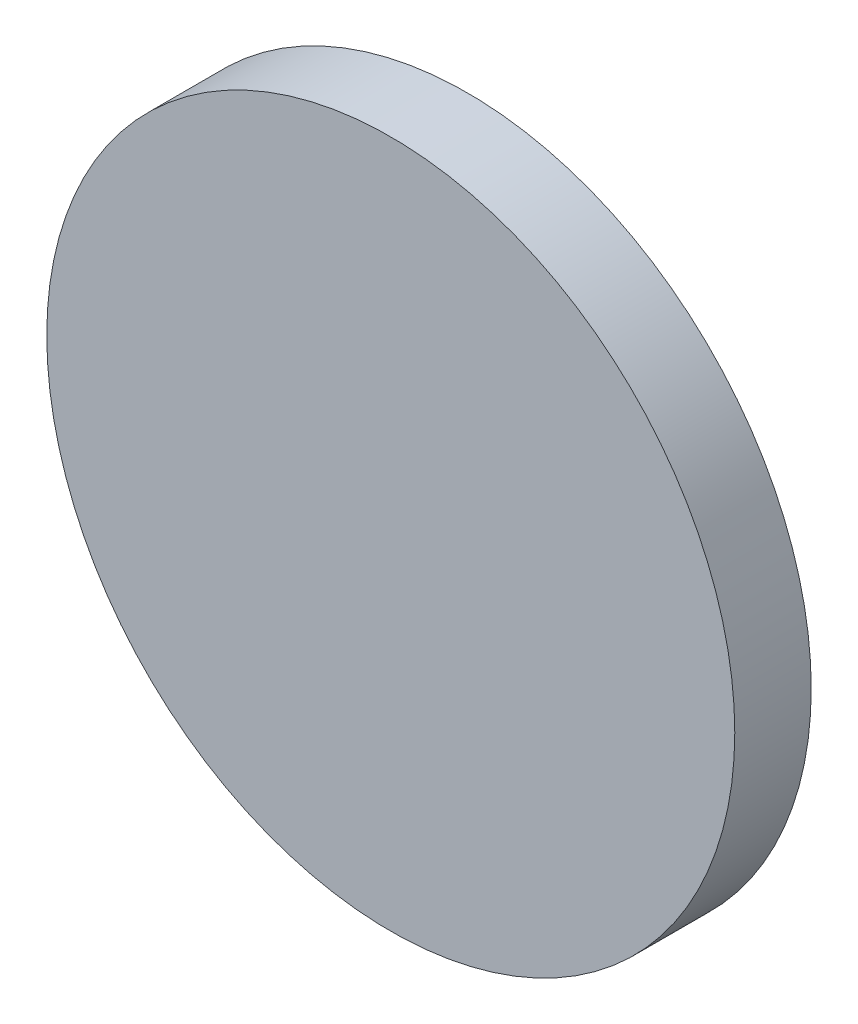
SolidWorks part; units mm, degrees
ref_plane "Front Plane" through (0, 0, 0) normal (0, 0, 1) x (1, 0, 0)
ref_plane "Top Plane" through (0, 0, 0) normal (0, 1, 0) x (1, 0, 0)
ref_plane "Right Plane" through (0, 0, 0) normal (1, 0, 0) x (0, 0, -1)
sketch "Sketch1" plane through (0, 0, 0) normal (0, 0, 1) x (1, 0, 0)
  circle A0 centre (0, 0) radius 114.3
  dimension "D1" = 228.6
extrude "Boss-Extrude1" add sketch "Sketch1" along normal blind 25.4
